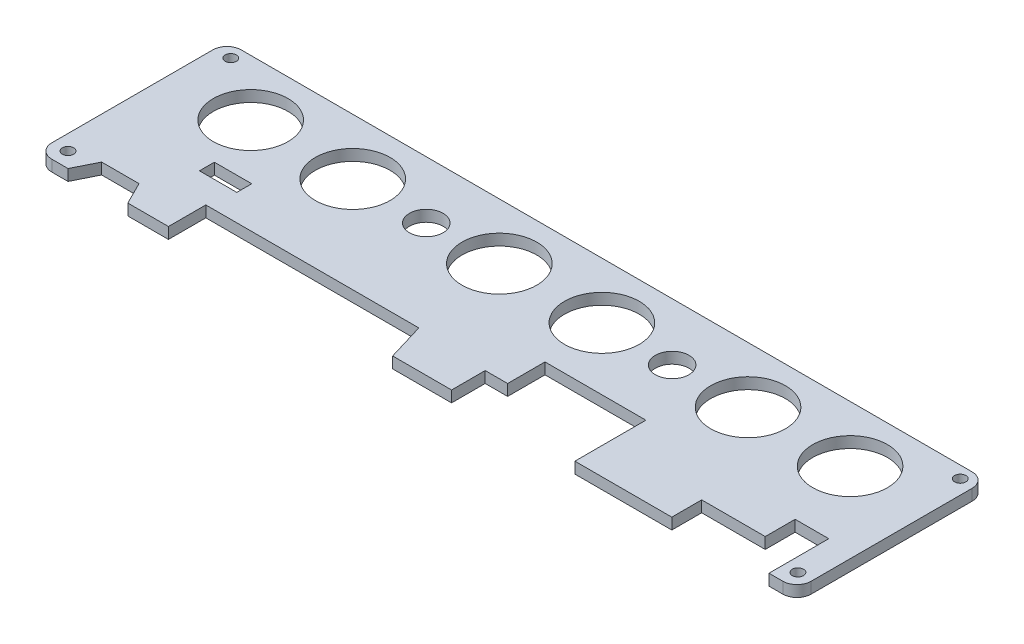
SolidWorks part; units mm, degrees
ref_plane "前视基准面" through (0, 0, 0) normal (0, 0, 1) x (1, 0, 0)
ref_plane "上视基准面" through (0, 0, 0) normal (0, 1, 0) x (1, 0, 0)
ref_plane "右视基准面" through (0, 0, 0) normal (1, 0, 0) x (0, 0, -1)
sketch "草图1" plane through (0, 0, 0) normal (0, 1, 0) x (1, 0, 0)
  line L0 (195.7, 0) -> (195.7, 16)
  line L1 (0, 0) -> (203.2, 0)
  line L2 (0, 0) -> (0, 50.673)
  line L3 (0, 50.673) -> (203.2, 50.673)
  line L4 (203.2, 0) -> (203.2, 50.673)
  line L5 (186.7, 16) -> (195.7, 16)
  line L6 (186.7, 16) -> (186.7, 0)
  line L7 (169.7, 0) -> (169.7, 8)
  line L8 (169.7, 8) -> (186.7, 8)
  line L9 (143.764, 0) -> (143.764, 19)
  line L10 (143.764, 19) -> (116.764, 19)
  line L11 (116.764, 19) -> (116.764, 9)
  line L12 (116.764, 9) -> (110.764, 9)
  line L13 (110.764, 9) -> (110.764, 0)
  line L14 (35, 0) -> (35, 10)
  line L15 (26.242, 21.05) -> (36.242, 21.05)
  line L16 (26.242, 21.05) -> (26.242, 17.05)
  line L17 (26.242, 17.05) -> (36.242, 17.05)
  line L18 (36.242, 21.05) -> (36.242, 17.05)
  line L19 (26.242, 21.05) -> (36.242, 17.05) construction
  line L20 (26.242, 17.05) -> (36.242, 21.05) construction
  line L21 (11.129, 6) -> (21.129, 6)
  line L22 (11.129, 6) -> (11.129, 2.9901)
  line L23 (11.129, 6) -> (8.129, 0)
  line L24 (21.129, 6) -> (21.129, 2.9901)
  line L25 (21.129, 6) -> (24.129, 0)
  line L26 (81, 10) -> (92, 10)
  line L27 (11.129, 6) -> (21.129, 6)
  line L28 (11.129, 6) -> (11.129, 0)
  line L29 (11.129, 0) -> (21.129, 0)
  line L30 (21.129, 6) -> (21.129, 0)
  line L31 (35, 10) -> (61.6204, 10)
  line L32 (92, 10) -> (92, 0)
  line L33 (61.6204, 10) -> (79.6204, 10)
  line L34 (92, 10) -> (95, 0)
  line L35 (79.6204, 10) -> (81, 10)
  line L36 (81, 10) -> (81, 0)
  circle A0 centre (4.064, 4.064) radius 1.5
  circle A1 centre (4.318, 47.371) radius 1.5
  circle A2 centre (199.39, 47.498) radius 1.5
  circle A3 centre (199.39, 4.064) radius 1.5
  circle A4 centre (21.336, 35.673) radius 10
  circle A5 centre (48.641, 35.673) radius 10
  circle A6 centre (87.884, 35.673) radius 10
  circle A7 centre (115.316, 35.673) radius 10
  circle A8 centre (154.432, 35.673) radius 10
  circle A9 centre (181.737, 35.673) radius 10
  circle A10 centre (68.691, 35.306) radius 4.5
  circle A11 centre (134.493, 35.306) radius 4.5
  point P42 (31.242, 19.05)
  point P47 (16.129, 3.683)
  point P62 (92, 0)
  dimension "D5" = 3
  dimension "D8" = 3
  dimension "D11" = 3
  dimension "D14" = 3
  dimension "D17" = 20
  dimension "D25" = 9
  dimension "D26" = 9
  dimension "D1" = 203.2
  dimension "D2" = 50.673
  dimension "D3" = 4.064
  dimension "D4" = 4.064
  dimension "D6" = 4.318
  dimension "D7" = 3.302
  dimension "D9" = 3.81
  dimension "D10" = 3.175
  dimension "D12" = 3.81
  dimension "D13" = 4.064
  dimension "D15" = 15
  dimension "D16" = 21.336
  dimension "D18" = 27.305
  dimension "D19" = 39.243
  dimension "D20" = 27.432
  dimension "D21" = 21.463
  dimension "D22" = 27.305
  dimension "D23" = 15.367
  dimension "D24" = 68.691
  dimension "D27" = 68.707
  dimension "D28" = 7.5
  dimension "D29" = 9
  dimension "D30" = 16
  dimension "D31" = 26
  dimension "D32" = 8
  dimension "D33" = 33
  dimension "D34" = 27
  dimension "D35" = 19
  dimension "D36" = 9
  dimension "D37" = 59.436
  dimension "D38" = 31.242
  dimension "D39" = 19.05
  dimension "D40" = 4
  dimension "D41" = 10
  dimension "D42" = 3.683
  dimension "D43" = 16.129
  dimension "D44" = 10
  dimension "D45" = 10
  dimension "D46" = 10
  dimension "D47" = 46
  dimension "D48" = 35
  dimension "D49" = 10
  dimension "D50" = 3
  dimension "D51" = 3
  dimension "D52" = 6
  dimension "D53" = 92
  dimension "D54" = 3
extrude "凸台-拉伸1" add sketch "草图1" along normal blind 3
fillet "圆角1" radius 3.8 4 edges at (203.2, 1.5, -50.673) (203.2, 1.5, 0) (0, 1.5, 0) (0, 1.5, -50.673)
